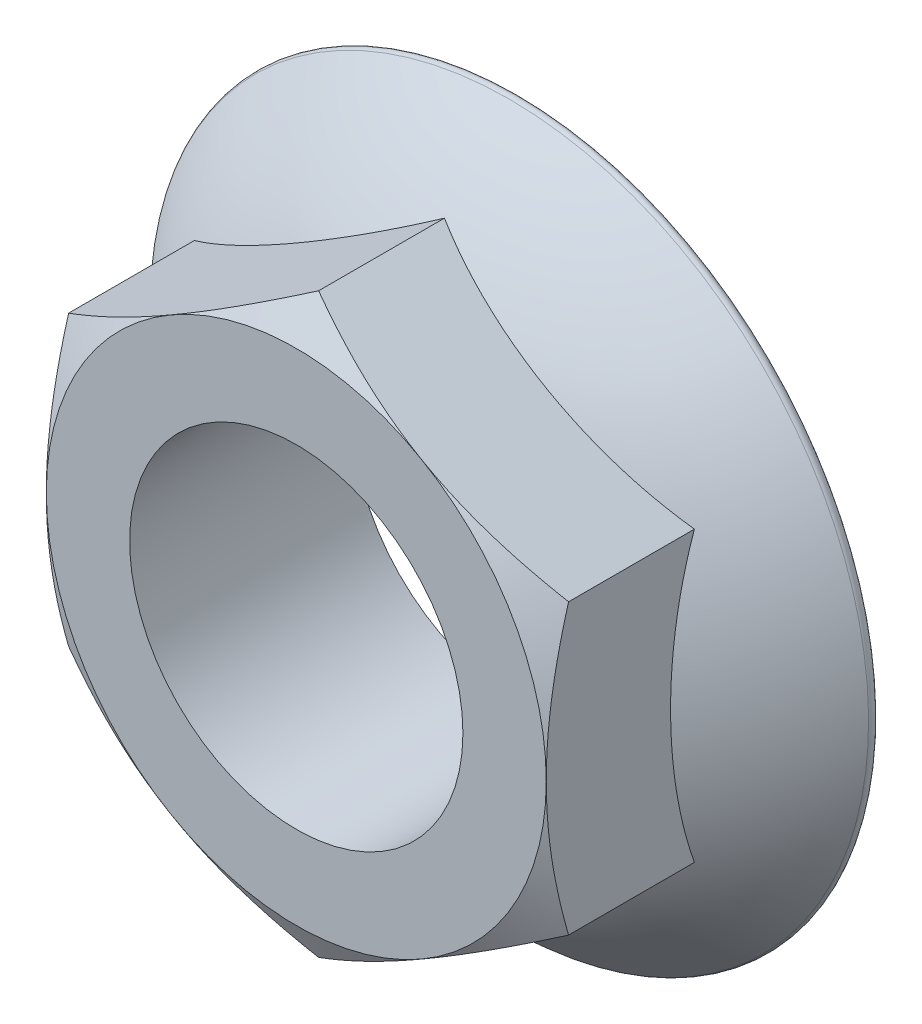
SolidWorks part; units mm, degrees
ref_plane "Front Plane" through (0, 0, 0) normal (0, 0, 1) x (1, 0, 0)
ref_plane "Top Plane" through (0, 0, 0) normal (0, 1, 0) x (1, 0, 0)
ref_plane "Right Plane" through (0, 0, 0) normal (1, 0, 0) x (0, 0, -1)
sketch "Sketch1" plane through (0, 0, 0) normal (0, 0, 1) x (1, 0, 0)
  line L1 (22.5, -12.9904) -> (22.5, 12.9904)
  line L2 (22.5, 12.9904) -> (0, 25.9808)
  line L3 (0, 25.9808) -> (-22.5, 12.9904)
  line L4 (-22.5, 12.9904) -> (-22.5, -12.9904)
  line L5 (-22.5, -12.9904) -> (0, -25.9808)
  line L6 (0, -25.9808) -> (22.5, -12.9904)
  circle A0 centre (0, 0) radius 22.5 construction
  dimension "D1" = 45
extrude "Boss-Extrude1" add sketch "Sketch1" along normal blind 20
sketch "Sketch2" plane through (0, 0, 0) normal (1, 0, 0) x (0, 0, -1)
  line L0 (0, 0) -> (-12, 0)
  line L1 (0, -31.95) -> (0, 0)
  arc A0 (-12, 0) -> (-0.8208, -32.3335) centre (20.4759, -6.8709) ccw
  arc A1 (-0.8208, -32.3335) -> (0, -31.95) centre (-0.5, -31.95) ccw
  dimension "D2" = 0.5
  dimension "D1" = 12
  dimension "D3" = 31.95
revolve "Revolve1" add sketch "Sketch2" angle 360 about L0
sketch "Sketch5" plane through (0, 0, 20) normal (0, 0, 1) x (1, 0, 0)
  circle A0 centre (0, 0) radius 22.5
extrude "Cut-Extrude1" cut sketch "Sketch5" against normal blind 20 draft 60 flip side to cut
sketch "Sketch6" plane through (0, 0, 20) normal (0, 0, 1) x (1, 0, 0)
  circle A0 centre (0, 0) radius 15
  dimension "D1" = 30
extrude "Cut-Extrude2" cut sketch "Sketch6" against normal through all
cosmetic thread "Cosmetic Thread1" parameters "D2"=31.75
